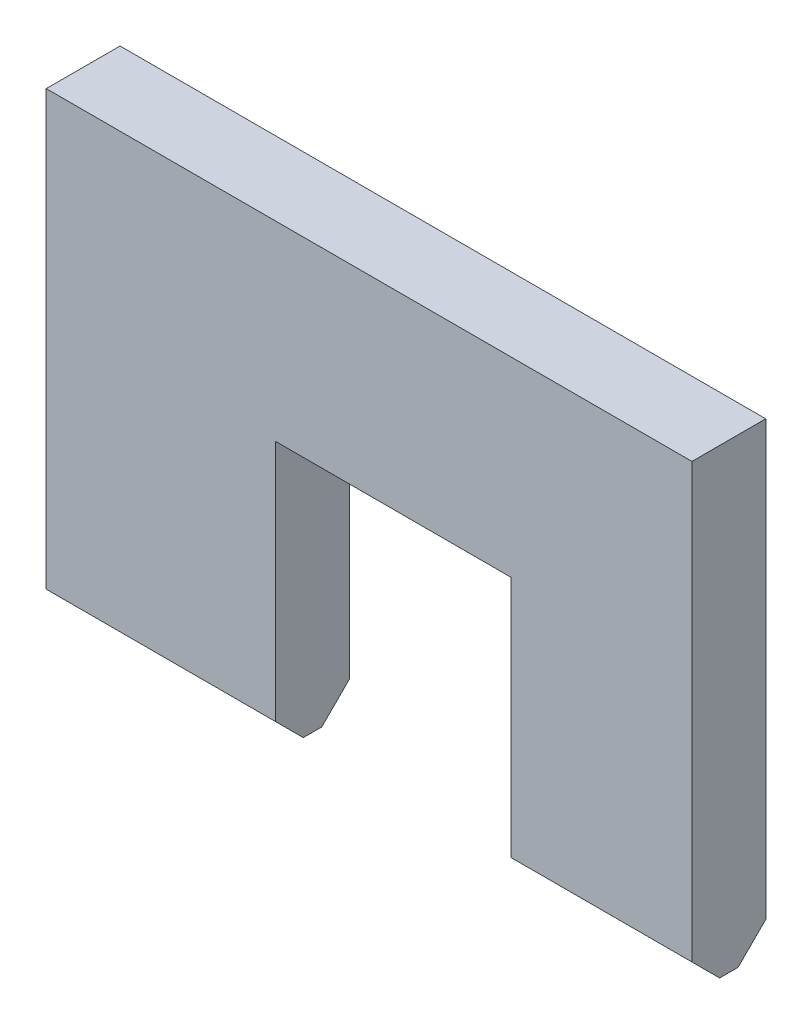
SolidWorks part; units mm, degrees
ref_plane "前视基准面" through (0, 0, 0) normal (0, 0, 1) x (1, 0, 0)
ref_plane "上视基准面" through (0, 0, 0) normal (0, 1, 0) x (1, 0, 0)
ref_plane "右视基准面" through (0, 0, 0) normal (1, 0, 0) x (0, 0, -1)
sketch "草图1" plane through (0, 0, 0) normal (0, 1, 0) x (1, 0, 0)
  line L1 (17.5, -2) -> (-17.5, -2)
  line L2 (17.5, -2) -> (17.5, 2)
  line L3 (17.5, 2) -> (-17.5, 2)
  line L4 (-17.5, -2) -> (-17.5, 2)
  line L5 (17.5, -2) -> (-17.5, 2) construction
  line L6 (17.5, 2) -> (-17.5, -2) construction
  point P0 (0, 0)
  dimension "D1" = 35
  dimension "D2" = 4
extrude "凸台-拉伸1" add sketch "草图1" along normal blind 25 contours L1 L4 L3 L2
chamfer "倒角1" distance 1.5 angle 45 2 edges at (0, 0, 2) (0, 0, -2)
sketch "草图2" plane through (0, 0, -2) normal (0, 0, -1) x (-1, 0, 0)
  line L1 (5.0662, -2.6534) -> (-7.678, -2.6534)
  line L2 (5.0662, -2.6534) -> (5.0662, 14.6557)
  line L3 (5.0662, 14.6557) -> (-7.678, 14.6557)
  line L4 (-7.678, -2.6534) -> (-7.678, 14.6557)
extrude "切除-拉伸1" cut sketch "草图2" against normal blind 10
